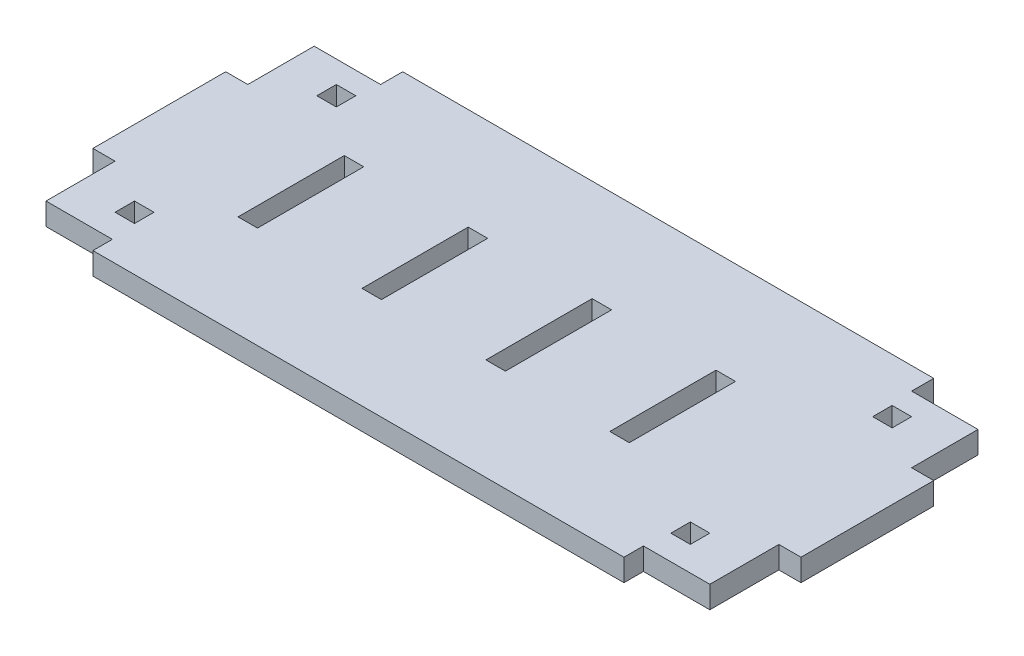
SolidWorks part; units mm, degrees
other "tab2"
ref_plane "Front Plane" through (0, 0, 0) normal (0, 0, 1) x (1, 0, 0)
ref_plane "Top Plane" through (0, 0, 0) normal (0, 1, 0) x (1, 0, 0)
ref_plane "Right Plane" through (0, 0, 0) normal (1, 0, 0) x (0, 0, -1)
sketch "Sketch1" plane through (0, 0, 0) normal (0, 1, 0) x (1, 0, 0)
  line L1 (-95.25, -44.45) -> (95.25, -44.45)
  line L2 (-95.25, -44.45) -> (-95.25, 44.45)
  line L3 (-95.25, 44.45) -> (95.25, 44.45)
  line L4 (95.25, -44.45) -> (95.25, 44.45)
  line L5 (-95.25, -44.45) -> (95.25, 44.45) construction
  line L6 (-95.25, 44.45) -> (95.25, -44.45) construction
  point P0 (0, 0)
  dimension "D1" = 190.5
  dimension "D2" = 88.9
extrude "Boss-Extrude1" add sketch "Sketch1" along normal blind 6.35
sketch "Sketch2" plane through (0, 6.35, 0) normal (0, 1, 0) x (1, 0, 0)
  line L0 (-55, 0) -> (55, 0) construction
  line L1 (-63.754, 15.24) -> (-58.166, 15.24)
  line L2 (-63.754, 15.24) -> (-63.754, -15.24)
  line L3 (-63.754, -15.24) -> (-58.166, -15.24)
  line L4 (-58.166, 15.24) -> (-58.166, -15.24)
  line L5 (-63.754, 15.24) -> (-58.166, -15.24) construction
  line L6 (-63.754, -15.24) -> (-58.166, 15.24) construction
  line L7 (0, -55) -> (0, 55) construction
  line L8 (-28.194, 15.24) -> (-22.606, 15.24)
  line L9 (-28.194, 15.24) -> (-28.194, -15.24)
  line L10 (-28.194, -15.24) -> (-22.606, -15.24)
  line L11 (-22.606, 15.24) -> (-22.606, -15.24)
  line L12 (-28.194, 15.24) -> (-22.606, -15.24) construction
  line L13 (-28.194, -15.24) -> (-22.606, 15.24) construction
  line L14 (7.366, 15.24) -> (12.954, 15.24)
  line L15 (7.366, 15.24) -> (7.366, -15.24)
  line L16 (7.366, -15.24) -> (12.954, -15.24)
  line L17 (12.954, 15.24) -> (12.954, -15.24)
  line L18 (7.366, 15.24) -> (12.954, -15.24) construction
  line L19 (7.366, -15.24) -> (12.954, 15.24) construction
  line L20 (42.926, 15.24) -> (48.514, 15.24)
  line L21 (42.926, 15.24) -> (42.926, -15.24)
  line L22 (42.926, -15.24) -> (48.514, -15.24)
  line L23 (48.514, 15.24) -> (48.514, -15.24)
  line L24 (42.926, 15.24) -> (48.514, -15.24) construction
  line L25 (42.926, -15.24) -> (48.514, 15.24) construction
  line L26 (-60.96, 0) -> (-25.4, 0) construction
  point P0 (-60.96, 0)
  point P10 (-25.4, 0)
  point P15 (10.16, 0)
  point P20 (45.72, 0)
  dimension "D1" = 5.588
  dimension "D2" = 30.48
  dimension "D3" = 25.4
  dimension "D5" = 35.56
  dimension "D4" = 4
extrude "hole" cut sketch "Sketch2" against normal blind 6.35
sketch "Sketch3" plane through (-95.25, 0, 0) normal (-1, 0, 0) x (0, 0, 1)
  line L0 (-44.45, 6.35) -> (44.45, 6.35) construction
  line L1 (-19.05, 6.35) -> (19.05, 6.35)
  line L2 (-19.05, 6.35) -> (-19.05, 0)
  line L3 (-19.05, 0) -> (19.05, 0)
  line L4 (19.05, 6.35) -> (19.05, 0)
  line L5 (-44.45, 0) -> (44.45, 0) construction
  line L6 (-44.45, 6.35) -> (-44.45, 0) construction
  line L7 (44.45, 6.35) -> (44.45, 0) construction
  point P8 (-44.45, 3.175)
  dimension "D1" = 25.4
  dimension "D2" = 25.4
extrude "tab1" add sketch "Sketch3" along normal blind 6.35
sketch "Sketch4" plane through (95.25, 0, 0) normal (1, 0, 0) x (0, 0, -1)
  line L0 (-44.45, 6.35) -> (44.45, 6.35) construction
  line L1 (-19.05, 6.35) -> (19.05, 6.35)
  line L2 (-19.05, 6.35) -> (-19.05, 0)
  line L3 (-19.05, 0) -> (19.05, 0)
  line L4 (19.05, 6.35) -> (19.05, 0)
  line L5 (-44.45, 0) -> (44.45, 0) construction
  line L6 (-44.45, 6.35) -> (-44.45, 0) construction
  line L7 (44.45, 6.35) -> (44.45, 0) construction
  dimension "D1" = 25.4
  dimension "D2" = 25.4
extrude "tab2" add sketch "Sketch4" along normal blind 6.35
sketch "Sketch5" plane through (0, 6.35, 0) normal (0, 1, 0) x (1, 0, 0)
  line L0 (95.25, 44.45) -> (-95.25, 44.45) construction
  line L1 (-82.55, 31.75) -> (-76.962, 31.75)
  line L2 (-82.55, 31.75) -> (-82.55, 26.162)
  line L3 (-82.55, 26.162) -> (-76.962, 26.162)
  line L4 (-76.962, 31.75) -> (-76.962, 26.162)
  line L5 (-95.25, 44.45) -> (-95.25, 19.05) construction
  dimension "D1" = 5.588
  dimension "D2" = 5.588
  dimension "D3" = 12.7
  dimension "D4" = 12.7
extrude "dowel1" cut sketch "Sketch5" against normal up to next (6.35 mm away)
mirror "Mirror1" about plane through (0, 0, 0) normal (1, 0, 0) of "dowel1"
mirror "Mirror2" about plane through (0, 0, 0) normal (0, 0, 1) of "Mirror1", "dowel1"
sketch "Sketch6" plane through (0, 6.35, 0) normal (0, 1, 0) x (1, 0, 0)
  line L1 (-95.25, -44.45) -> (-76.2, -44.45)
  line L2 (-95.25, -44.45) -> (-95.25, -38.862)
  line L3 (-95.25, -38.862) -> (-76.2, -38.862)
  line L4 (-76.2, -44.45) -> (-76.2, -38.862)
  line L5 (95.25, -44.45) -> (76.2, -44.45)
  line L6 (95.25, -44.45) -> (95.25, -38.862)
  line L7 (95.25, -38.862) -> (76.2, -38.862)
  line L8 (76.2, -44.45) -> (76.2, -38.862)
  line L9 (-95.25, 44.45) -> (-76.2, 44.45)
  line L10 (-95.25, 44.45) -> (-95.25, 38.1)
  line L11 (-95.25, 38.1) -> (-76.2, 38.1)
  line L12 (-76.2, 44.45) -> (-76.2, 38.1)
  line L13 (95.25, 44.45) -> (76.2, 44.45)
  line L14 (95.25, 44.45) -> (95.25, 38.1)
  line L15 (95.25, 38.1) -> (76.2, 38.1)
  line L16 (76.2, 44.45) -> (76.2, 38.1)
  dimension "D1" = 5.588
  dimension "D2" = 19.05
  dimension "D3" = 19.05
  dimension "D4" = 6.35
extrude "Cut-Extrude1" cut sketch "Sketch6" against normal through all
